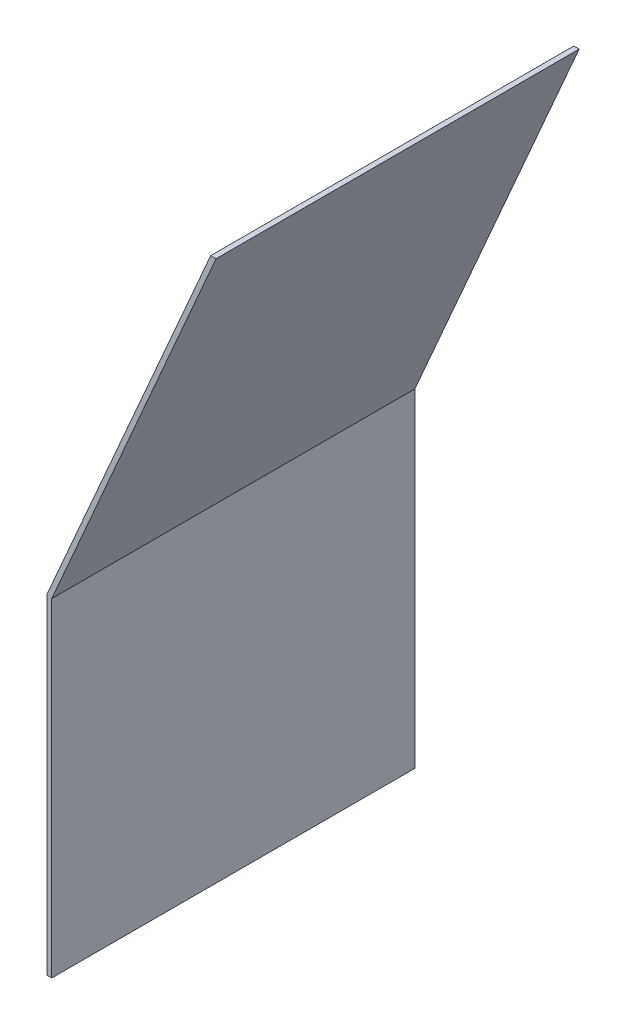
SolidWorks part; units mm, degrees
material "Plain Carbon Steel"
ref_plane "Front Plane" through (0, 0, 0) normal (0, 0, 1) x (1, 0, 0)
ref_plane "Top Plane" through (0, 0, 0) normal (0, 1, 0) x (1, 0, 0)
ref_plane "Right Plane" through (0, 0, 0) normal (1, 0, 0) x (0, 0, -1)
sketch "Sketch1" plane through (0, 0, 0) normal (0, 0, 1) x (1, 0, 0)
  line L0 (0, 0) -> (1.5189, 0)
  line L1 (1.5189, 0) -> (1.5189, 101.6)
  line L2 (1.5189, 101.6) -> (52.3226, 217.9958)
  line L3 (52.3226, 217.9958) -> (50.6653, 217.9958)
  line L4 (50.6653, 217.9958) -> (0, 101.917)
  line L5 (0, 101.917) -> (0, 0)
  point P3 (0, -0.9233)
  point P8 (2.1927, 15.2855)
  point P9 (169.2838, 279.4)
  dimension "D1" = 1.5189
  dimension "D2" = 101.6
  dimension "D3" = 127
  dimension "D4" = 156.42
  dimension "D5" = 1.5189
extrude "Boss-Extrude1" add sketch "Sketch1" along normal blind 112.268
